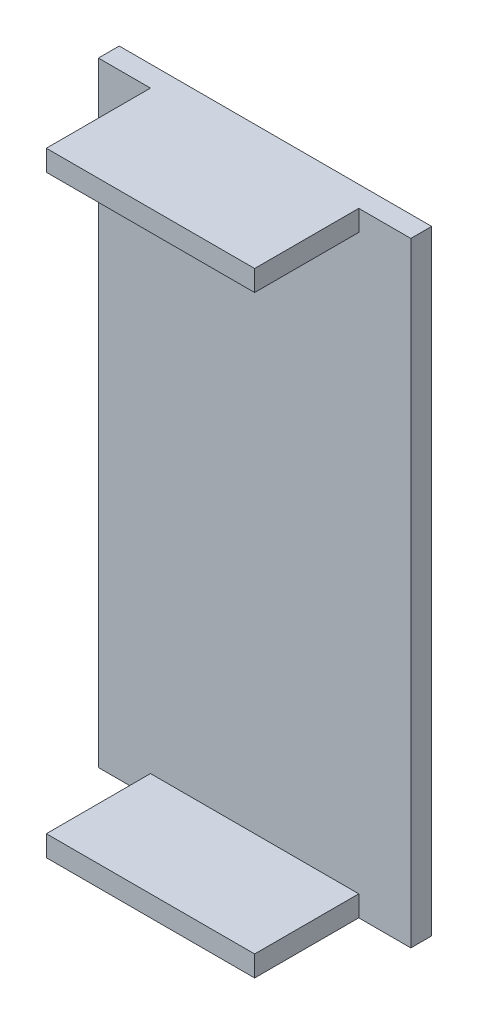
SolidWorks part; units mm, degrees
ref_plane "Front Plane" through (0, 0, 0) normal (0, 0, 1) x (1, 0, 0)
ref_plane "Top Plane" through (0, 0, 0) normal (0, 1, 0) x (1, 0, 0)
ref_plane "Right Plane" through (0, 0, 0) normal (1, 0, 0) x (0, 0, -1)
sketch "Sketch1" plane through (0, 0, 0) normal (0, 0, 1) x (1, 0, 0)
  line L1 (0, 0) -> (30, 0)
  line L2 (0, 0) -> (0, 59)
  line L3 (0, 59) -> (30, 59)
  line L4 (30, 0) -> (30, 59)
  dimension "D1" = 59
  dimension "D2" = 30
extrude "Boss-Extrude1" add sketch "Sketch1" along normal blind 2
sketch "Sketch2" plane through (0, 0, 2) normal (0, 0, 1) x (1, 0, 0)
  line L0 (0, 59) -> (5, 59)
  line L1 (30, 59) -> (0, 59) construction
  line L2 (30, 59) -> (25, 59)
  line L3 (0, 0) -> (5, 0)
  line L4 (5, 59) -> (25, 59)
  line L5 (5, 59) -> (5, 57)
  line L6 (5, 57) -> (25, 57)
  line L7 (25, 59) -> (25, 57)
  line L8 (0, 0) -> (30, 0) construction
  line L9 (30, 0) -> (25, 0)
  line L11 (25, 0) -> (5, 0)
  line L12 (25, 0) -> (25, 2)
  line L13 (25, 2) -> (5, 2)
  line L14 (5, 0) -> (5, 2)
  line M2 (0, 0) -> (30, 0)
  line M4 (30, 59) -> (0, 59)
  dimension "D1" = 5
  dimension "D2" = 5
  dimension "D3" = 2
  dimension "D4" = 5
  dimension "D5" = 2
extrude "Boss-Extrude2" add sketch "Sketch2" along normal blind 10 contours L7 L5 L6 M4 | L14 L12 L13 M2
